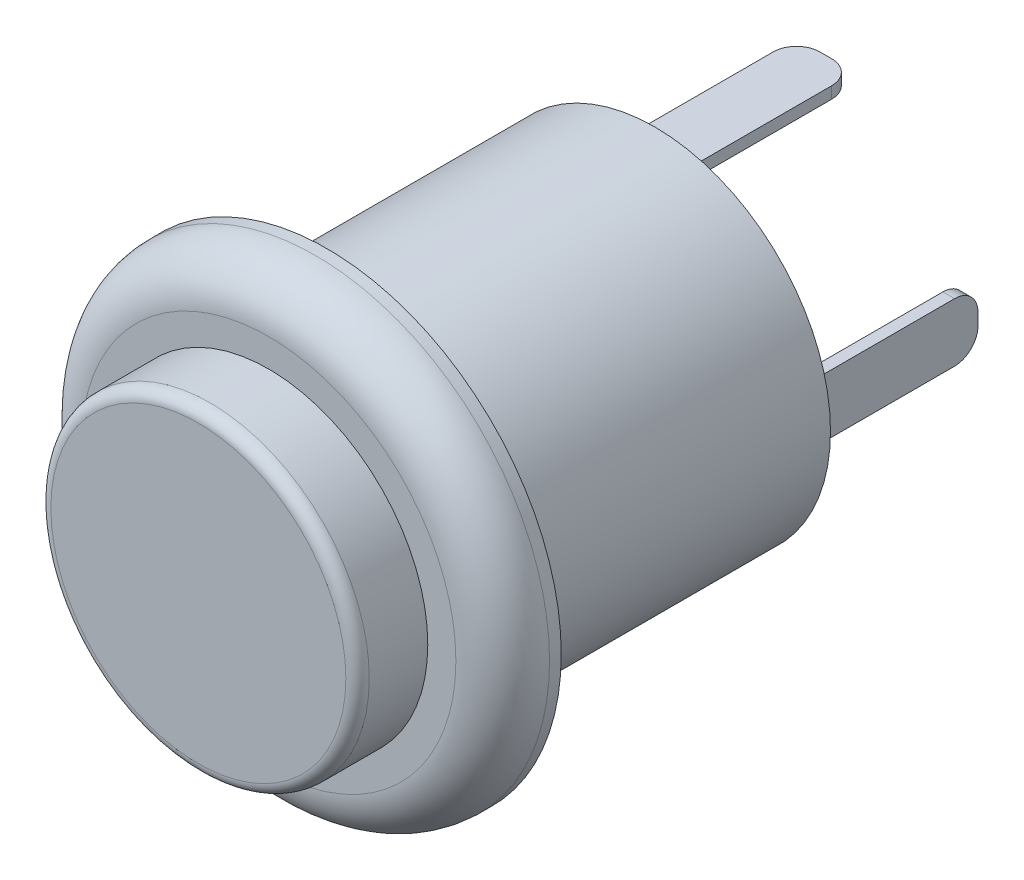
SolidWorks part; units mm, degrees
ref_plane "正面" through (0, 0, 0) normal (0, 0, 1) x (1, 0, 0)
ref_plane "平面" through (0, 0, 0) normal (0, 1, 0) x (1, 0, 0)
ref_plane "右側面" through (0, 0, 0) normal (1, 0, 0) x (0, 0, -1)
ref_plane "平面1" through (0, 0, 0) normal (0, 0, 1) x (1, 0, 0)
sketch "ｽｹｯﾁ1" plane through (0, 0, 0) normal (0, 0, 1) x (1, 0, 0)
  circle A0 centre (0, 0) radius 7.5
  dimension "D1" = 15
extrude "ﾎﾞｽ - 押し出し1" add sketch "ｽｹｯﾁ1" along normal blind 14
sketch "ｽｹｯﾁ2" plane through (0, 0, 14) normal (0, 0, 1) x (1, 0, 0)
  circle A0 centre (0, 0) radius 10
  dimension "D1" = 20
extrude "ﾎﾞｽ - 押し出し2" add sketch "ｽｹｯﾁ2" along normal blind 2.5
sketch "ｽｹｯﾁ3" plane through (0, 0, 16.5) normal (0, 0, 1) x (1, 0, 0)
  circle A0 centre (0, 0) radius 6.8
  dimension "D1" = 13.6
extrude "ﾎﾞｽ - 押し出し3" add sketch "ｽｹｯﾁ3" along normal blind 3
sketch "ｽｹｯﾁ4" plane through (0, 0, 0) normal (0, 0, -1) x (-1, 0, 0)
  line L0 (-6.25, 0) -> (6.25, 0) construction
  line L1 (-6.5, 1.25) -> (-6, 1.25)
  line L2 (-6.5, 1.25) -> (-6.5, -1.25)
  line L3 (-6.5, -1.25) -> (-6, -1.25)
  line L4 (-6, 1.25) -> (-6, -1.25)
  line L5 (-6.5, 1.25) -> (-6, -1.25) construction
  line L6 (-6.5, -1.25) -> (-6, 1.25) construction
  line L7 (6.5, 1.25) -> (6, 1.25)
  line L8 (6.5, 1.25) -> (6.5, -1.25)
  line L9 (6.5, -1.25) -> (6, -1.25)
  line L10 (6, 1.25) -> (6, -1.25)
  line L11 (6.5, 1.25) -> (6, -1.25) construction
  line L12 (6.5, -1.25) -> (6, 1.25) construction
  line L13 (-1.25, 6.5) -> (1.25, 6.5)
  line L14 (-1.25, 6.5) -> (-1.25, 6)
  line L15 (-1.25, 6) -> (1.25, 6)
  line L16 (1.25, 6.5) -> (1.25, 6)
  line L17 (-1.25, 6.5) -> (1.25, 6) construction
  line L18 (-1.25, 6) -> (1.25, 6.5) construction
  line L19 (-1.25, -6) -> (1.25, -6)
  line L20 (-1.25, -6) -> (-1.25, -6.5)
  line L21 (-1.25, -6.5) -> (1.25, -6.5)
  line L22 (1.25, -6) -> (1.25, -6.5)
  line L23 (-1.25, -6) -> (1.25, -6.5) construction
  line L24 (-1.25, -6.5) -> (1.25, -6) construction
  line L25 (0, 6.25) -> (0, -6.25) construction
  point P0 (-6.25, 0)
  point P5 (6.25, 0)
  point P10 (0, 6.25)
  point P15 (0, -6.25)
  point P24 (0, 0)
  point P25 (0, 0)
  dimension "D1" = 2.5
  dimension "D2" = 0.5
  dimension "D3" = 2.5
  dimension "D4" = 0.5
  dimension "D5" = 2.5
  dimension "D6" = 0.5
  dimension "D7" = 2.5
  dimension "D8" = 0.5
  dimension "D9" = 6
  dimension "D10" = 6
extrude "ﾎﾞｽ - 押し出し4" add sketch "ｽｹｯﾁ4" along normal blind 7.3
fillet "ﾌｨﾚｯﾄ1" radius 1 8 edges at (-1.25, 6.25, -7.3) (1.25, 6.25, -7.3) (-6.25, 1.25, -7.3) (-6.25, -1.25, -7.3) (-1.25, -6.25, -7.3) (1.25, -6.25, -7.3) (6.25, -1.25, -7.3) (6.25, 1.25, -7.3)
fillet "ﾌｨﾚｯﾄ2" radius 0.5 1 edges at (6.8, 0, 19.5)
fillet "ﾌｨﾚｯﾄ3" radius 2 1 edges at (10, 0, 16.5)
sketch "ｽｹｯﾁ5" plane through (0, 0, 19.5) normal (0, 0, 1) x (1, 0, 0)
  text T0 "A" font "Century Gothic" height in points 30
